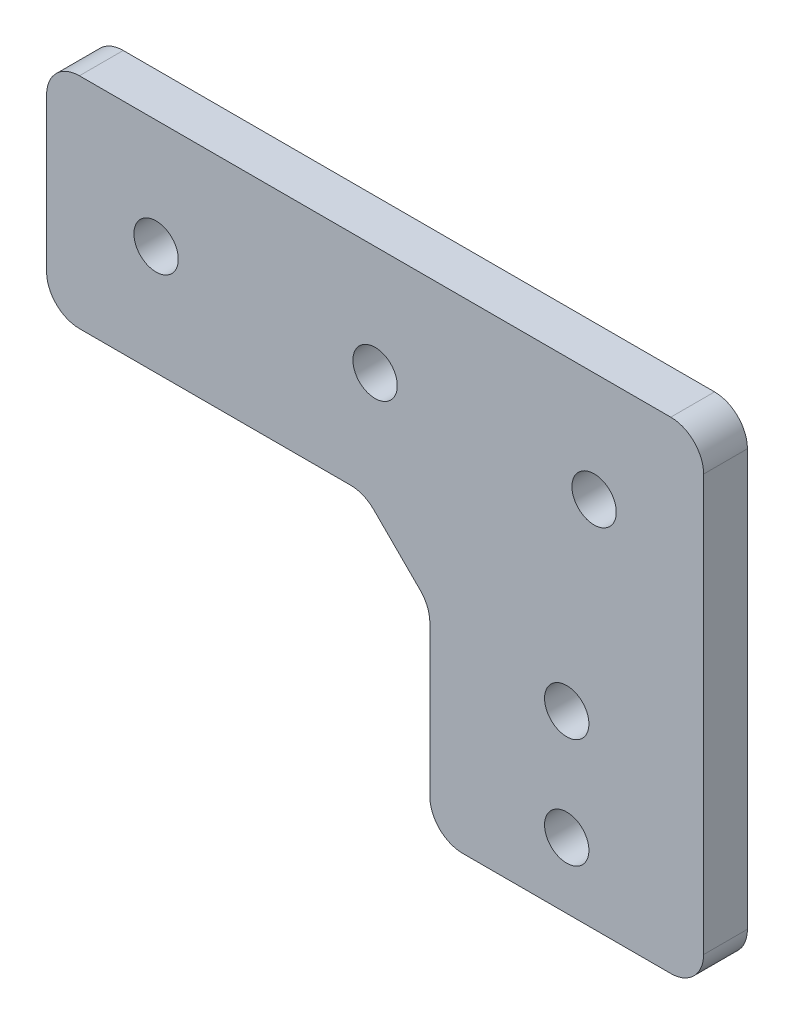
SolidWorks part; units mm, degrees
material "Thornel Mat VMA"
ref_plane "前视基准面" through (0, 0, 0) normal (0, 0, 1) x (1, 0, 0)
ref_plane "上视基准面" through (0, 0, 0) normal (0, 1, 0) x (1, 0, 0)
ref_plane "右视基准面" through (0, 0, 0) normal (1, 0, 0) x (0, 0, -1)
other "Configuration Table"
sketch "草图1" plane through (0, 0, 0) normal (0, 0, 1) x (1, 0, 0)
  line L0 (-35, 0) -> (0, 0)
  line L1 (0, 0) -> (0, -30)
  line L2 (0, -30) -> (25, -30)
  line L3 (25, -30) -> (25, 20)
  line L4 (25, 20) -> (-35, 20)
  line L5 (-35, 20) -> (-35, 0)
  dimension "D1" = 25
  dimension "D2" = 50
  dimension "D3" = 20
  dimension "D4" = 60
extrude "凸台-拉伸1" add sketch "草图1" along normal blind 4
sketch "草图2" plane through (0, 0, 0) normal (0, 0, -1) x (-1, 0, 0)
  line L0 (-15.3472, 38.4733) -> (-25, 20)
  line L1 (-25, -30) -> (-25, 20) construction
  line L2 (-8.7, 35) -> (-8.7, 20) construction
  line L3 (-2.0528, 38.4733) -> (7.6, 20)
  line L4 (-25, 20) -> (35, 20) construction
  line L5 (-25, 20) -> (7.6, 20)
  line L6 (-25, -30) -> (-25, 20) construction
  arc A0 (-2.0528, 38.4733) -> (-15.3472, 38.4733) centre (-8.7, 35) ccw
  dimension "D1" = 15
extrude "凸台-拉伸2" add sketch "草图2" against normal up to surface (4 mm away) up to face at (-3.3333, -3.3333, 4)
sketch "草图3" plane through (0, 0, 0) normal (0, 0, -1) x (-1, 0, 0)
  circle A0 centre (-8.7, 35) radius 5
  dimension "D1" = 10
extrude "切除-拉伸1" cut sketch "草图3" against normal up to surface (4 mm away) up to face at (-1.1333, 8.997, 4)
sketch "草图6" plane through (0, 0, 0) normal (0, 0, -1) x (-1, 0, 0)
  line L0 (-25, -30) -> (-25, 20) construction
  line L1 (-25, -24) -> (0, -24)
  line L2 (-25, -24) -> (-25, -30)
  line L3 (-25, -30) -> (0, -30)
  line L4 (0, -24) -> (0, -30)
  line L5 (0, -7.5) -> (0, -407.5) construction
  line L6 (0, -30) -> (-25, -30) construction
  dimension "D1" = 6
extrude "切除-拉伸4" cut sketch "草图6" against normal through all both and the other way through all
sketch "草图7" plane through (0, 0, 0) normal (0, 0, -1) x (-1, 0, 0)
  line L0 (35, 0) -> (0, 0) construction
  line L1 (-17.5, -18) -> (-7.5, -18) construction
  line L2 (-17.5, -18) -> (-17.5, -8) construction
  line L3 (-17.5, -8) -> (-7.5, -8) construction
  line L4 (-7.5, -18) -> (-7.5, -8) construction
  line L5 (-17.5, -18) -> (-7.5, -8) construction
  line L6 (-17.5, -8) -> (-7.5, -18) construction
  line L7 (-12.5, -24) -> (-12.5, -13) construction
  line L8 (-25, -24) -> (0, -24) construction
  circle A4 centre (-12.5, -8) radius 2.025
  circle A5 centre (-12.5, -18) radius 2.025
  point P0 (-12.5, -13)
  dimension "D4" = 4.05
  dimension "D1" = 10
  dimension "D2" = 10
  dimension "D3" = 8
extrude "切除-拉伸5" cut sketch "草图7" against normal through all both
sketch "草图9" plane through (0, 0, 0) normal (0, 0, -1) x (-1, 0, 0)
  line L0 (-20.8784, 37.8172) -> (-25, 20)
  line L1 (3.4784, 37.8172) -> (7.6, 20)
  line L2 (-25, 20) -> (7.6, 20)
  arc A0 (3.4784, 37.8172) -> (-20.8784, 37.8172) centre (-8.7, 35) ccw
  circle A1 centre (-8.7, 35) radius 5
  dimension "D1" = 25
  dimension "D2" = 10
extrude "凸台-拉伸3" add sketch "草图9" against normal up to surface (4 mm away) up to face at (10.475, -8, 4)
sketch "草图12" plane through (0, 0, 0) normal (0, 0, -1) x (-1, 0, 0)
  line L0 (35, 20) -> (35, 0) construction
  line L1 (-25, -24) -> (-25, 20) construction
  circle A0 centre (-15, 10) radius 2.025
  circle A1 centre (5, 10) radius 2.025
  circle A2 centre (25, 10) radius 2.025
  point P8 (35, 10)
  dimension "D1" = 4.05
  dimension "D2" = 10
  dimension "D3" = 20
  dimension "D4" = 20
extrude "切除-拉伸8" cut sketch "草图12" against normal through all both
sketch "草图13" plane through (0, 0, 0) normal (0, 0, -1) x (-1, 0, 0)
  line L0 (-25, 20) -> (7.6, 20)
  line L1 (7.6, 20) -> (3.4784, 37.8172) construction
  line L2 (7.6, 20) -> (3.4784, 37.8172)
  line L3 (-20.8784, 37.8172) -> (-25, 20) construction
  line L4 (-20.8784, 37.8172) -> (-25, 20)
  arc A0 (3.4784, 37.8172) -> (-20.8784, 37.8172) centre (-8.7, 35) ccw construction
  arc A1 (3.4784, 37.8172) -> (-20.8784, 37.8172) centre (-8.7, 35) ccw
extrude "切除-拉伸9" cut sketch "草图13" against normal through all both
sketch "草图14" plane through (0, 0, 0) normal (0, 0, -1) x (-1, 0, 0)
  line L0 (0, -6) -> (6, 0)
  line L1 (0, 0) -> (0, -24) construction
  line L2 (35, 0) -> (0, 0) construction
  line L3 (6, 0) -> (0, 0)
  line L4 (0, 0) -> (0, -6)
  dimension "D1" = 6
  dimension "D2" = 6
extrude "凸台-拉伸4" add sketch "草图14" against normal up to surface (4 mm away) up to face at (-3.3333, -1.3333, 4)
fillet "圆角1" radius 3 7 edges at (25, -24, 2) (0, -24, 2) (-6, 0, 2) (-35, 0, 2) (-35, 20, 2) (25, 20, 2) (0, -6, 2)
